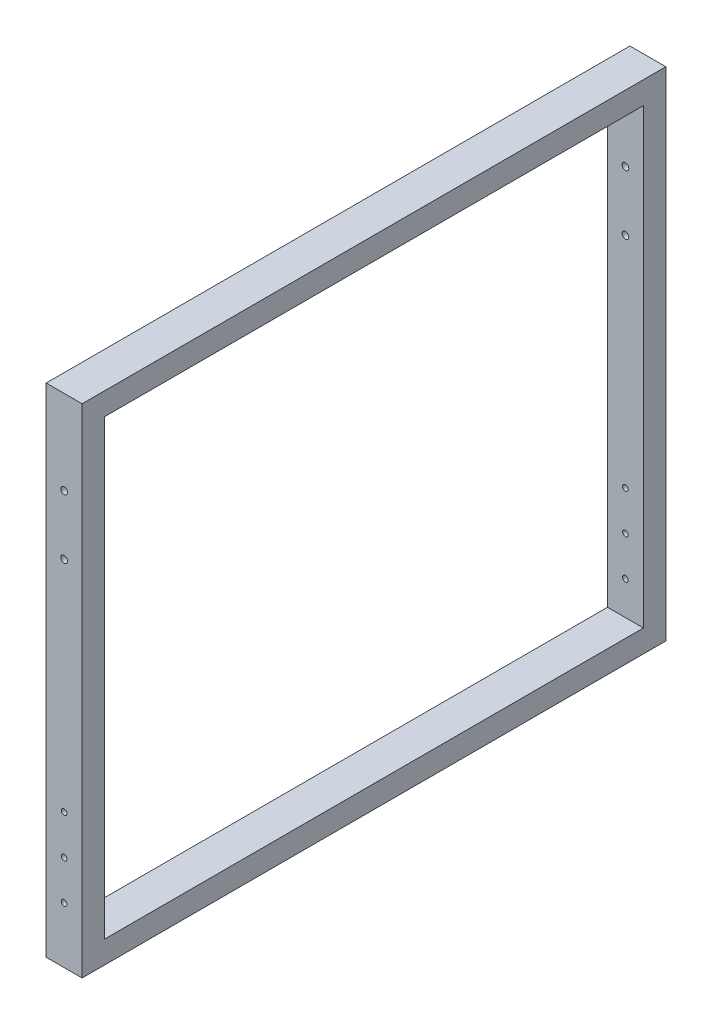
SolidWorks part; units mm, degrees
material "Balsa"
ref_plane "Front Plane" through (0, 0, 0) normal (0, 0, 1) x (1, 0, 0)
ref_plane "Top Plane" through (0, 0, 0) normal (0, 1, 0) x (1, 0, 0)
ref_plane "Right Plane" through (0, 0, 0) normal (1, 0, 0) x (0, 0, -1)
sketch "Sketch1" plane through (0, 0, 0) normal (1, 0, 0) x (0, 0, -1)
  line L0 (-250, 221.5) -> (-250, -221.5) construction
  line L1 (-240, -201.5) -> (240, -201.5)
  line L2 (-240, -201.5) -> (-240, 201.5)
  line L3 (-240, 201.5) -> (240, 201.5)
  line L4 (240, -201.5) -> (240, 201.5)
  line L5 (-240, -201.5) -> (240, 201.5) construction
  line L6 (-240, 201.5) -> (240, -201.5) construction
  line L7 (260, 221.5) -> (-260, 221.5)
  line L8 (260, 221.5) -> (260, -221.5)
  line L9 (260, -221.5) -> (-260, -221.5)
  line L10 (-260, 221.5) -> (-260, -221.5)
  line L11 (0, 201.5) -> (0, -201.5) construction
  point P0 (0, 0)
  point P10 (0, 201.5)
  point P11 (0, 221.5)
  dimension "D1" = 500
  dimension "D2" = 403
  dimension "D3" = 20
  dimension "D4" = 20
  dimension "D5" = 10
  dimension "D6" = 20
extrude "Boss-Extrude2" add sketch "Sketch1" along normal blind 32
sketch "Sketch2" plane through (0, 0, 260) normal (0, 0, 1) x (1, 0, 0)
  line L0 (16, 221.5) -> (16, -221.5) construction
  line L1 (32, 221.5) -> (0, 221.5) construction
  line L2 (32, -221.5) -> (0, -221.5) construction
  circle A0 centre (16, -171.5) radius 2.5
  circle A1 centre (16, -136.5) radius 2.5
  circle A2 centre (16, -101.5) radius 2.5
  dimension "D4" = 5
  dimension "D1" = 50
  dimension "D2" = 35
  dimension "D3" = 35
extrude "Cut-Extrude1" cut sketch "Sketch2" against normal blind 610
sketch "Sketch3" plane through (0, 0, 240) normal (0, 0, -1) x (-1, 0, 0)
  line L0 (-16, 201.5) -> (-16, -201.5) construction
  line L1 (-32, 201.5) -> (0, 201.5) construction
  line L2 (-32, -201.5) -> (0, -201.5) construction
  circle A0 centre (-16, 146.5) radius 3
  circle A1 centre (-16, 93.5) radius 3
  dimension "D1" = 6
  dimension "D2" = 53
  dimension "D3" = 55
extrude "Cut-Extrude2" cut sketch "Sketch3" along normal blind 641 and the other way blind 105
